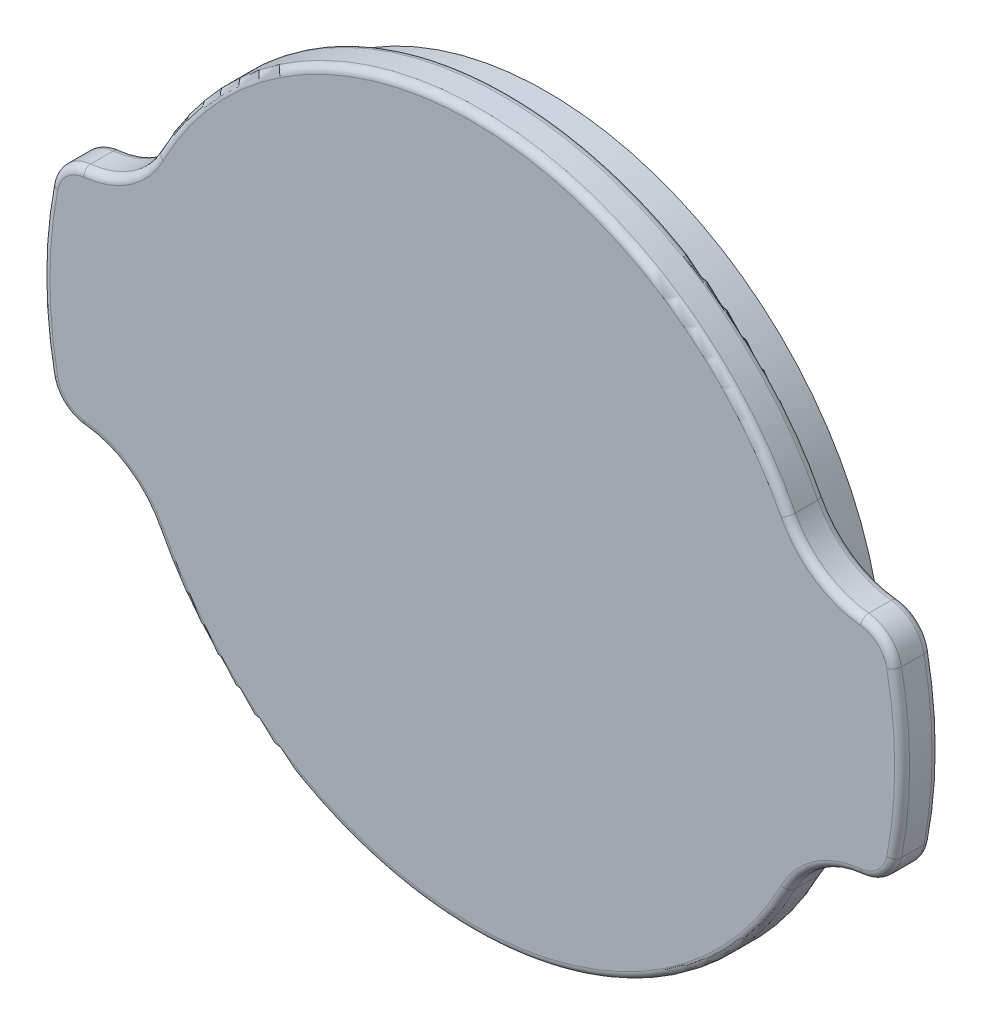
SolidWorks part; units mm, degrees
ref_plane "Front Plane" through (0, 0, 0) normal (0, 0, 1) x (1, 0, 0)
ref_plane "Top Plane" through (0, 0, 0) normal (0, 1, 0) x (1, 0, 0)
ref_plane "Right Plane" through (0, 0, 0) normal (1, 0, 0) x (0, 0, -1)
sketch "hopperTankCover" plane through (0, 0, 0) normal (0, 0, 1) x (1, 0, 0)
  circle A0 centre (0, 0) radius 95 construction
  circle A1 centre (0, 0) radius 95
extrude "Boss-Extrude1" add sketch "hopperTankCover" along normal blind 10
sketch "hopperTankCoverLip" plane through (0, 0, 0) normal (0, 0, -1) x (-1, 0, 0)
  circle A4 centre (0, 0) radius 85
  circle A5 centre (0, 0) radius 85
  circle A7 centre (0, 0) radius 89.9
  circle A8 centre (0, 0) radius 89.9
  dimension "hopperTankWallThickness" = 5
  dimension "generalFittingTolerance" = 0.1
extrude "Boss-Extrude2" add sketch "hopperTankCoverLip" along normal blind 10
sketch "hopperTankCoverHandle" plane through (0, 0, 10) normal (0, 0, 1) x (1, 0, 0)
  line L0 (-111.018, 30) -> (-90.1388, 30)
  line L1 (-111.018, -30) -> (-90.1388, -30)
  line L2 (0, 0) -> (0, 51.9864) construction
  line L3 (111.018, -30) -> (90.1388, -30)
  line L4 (111.018, 30) -> (90.1388, 30)
  arc A0 (90.1388, 30) -> (90.1388, -30) centre (0, 0) cw
  circle A1 centre (0, 0) radius 95 construction
  circle A2 centre (0, 0) radius 115
  arc A3 (-111.018, 30) -> (-111.018, -30) centre (0, 0) ccw
  arc A4 (-90.1388, 30) -> (-90.1388, -30) centre (0, 0) ccw
  arc A5 (111.018, 30) -> (111.018, -30) centre (0, 0) cw
  dimension "hopperTankCoverHandleLength" = 30
  dimension "D1" = 20
extrude "Boss-Extrude3" add sketch "hopperTankCoverHandle" against normal blind 10
fillet "Fillet1" radius 25 4 edges at (90.1388, -30, 5) (90.1388, 30, 5) (-90.1388, 30, 5) (-90.1388, -30, 5)
fillet "Fillet3" radius 10 4 edges at (-111.018, -30, 5) (-111.018, 30, 5) (111.018, 30, 5) (111.018, -30, 5)
fillet "Fillet4" radius 2 24 edges at (0, -95, 10) (0, -95, 0) (0, 95, 0) (0, 95, 10) (92.5575, -34.353, 10) (92.5575, 34.353, 0) (-92.5575, 34.353, 10) (-92.5575, -34.353, 0) (-115, 0, 10) (-115, 0, 0) (92.5575, 34.353, 10) (-92.5575, -34.353, 10) (115, 0, 10) (109.7868, -27.5691, 10) (109.7868, 27.5691, 10) (-109.7868, 27.5691, 10) (-109.7868, -27.5691, 10) (115, 0, 0) (92.5575, -34.353, 0) (-92.5575, 34.353, 0) (109.7868, -27.5691, 0) (109.7868, 27.5691, 0) (-109.7868, 27.5691, 0) (-109.7868, -27.5691, 0)
equation "\"pelletWidth\"= 13mm'The Width of the pellet to be dispensed"
equation "\"pelletLength\"= 26mm'The length of the pellet to be dispensed"
equation "\"pelletThickness\"= 13mm'The Thickness of the pellet to be dispensed"
equation "\"pelletRadius\"= 10mm'The roundness / radius of the pellet to be dispensed"
equation "\"rotatingPlateDiameter\"= 100mm'the diameter of the rotating plate"
equation "\"rotatingPlateHeight\"= (\"pelletThickness\"*0.9)'The thickness of the rotating plate"
equation "\"rotatingPlateDiameterAllowance\"= 0.5mm'Allowance around the edge of the rotating plate"
equation "\"rotatingPlateAgitatorDiameter\"= ( \"rotatingPlateDiameter\"-((\"pelletWidth\"*1.3)*2.5) )'The diameter of the \"agitator\" section of the rotating plate"
equation "\"rotatingPlateAgitatorHeight\"= 80mm'The height of the \"agitator\" section of the rotating plate"
equation "\"rotatingPlateAgitatorBladeThickness\"= 4mm'The thickness of the blade on the \"agitator\" section of the rotating plate"
equation "\"rotatingPlateAgitatorBladeDistance\"= ( (\"rotatingPlateAgitatorDiameter\"+ 20mm) - (\"rotatingPlateAgitatorDiameter\") )'The distance offset of the blade from the surface of the \"agitator\" section of the rotating plate"
equation "\"rotatingPlateAgitatorBladeBottomGap\"= ( \"pelletThickness\"*1.2 )'The gap between the bottom of the blade and the base of the plate on the \"agitator\" section of the rotating plate"
equation "\"rotatingPlateAgitatorBladesNumber\"= ( 3 )'The number of blades on the \"agitator\" section of the rotating plate"
equation "\"hopperBaseChamferAngle\"= 60deg'Angle of the chamfer of the Hopper base Toward the plate"
equation "\"hopperBaseLipOverhang\"= 5mm'The overhang amount of the hopper base lip"
equation "\"hopperBaseLipDepth\"= 5mm'The depth of the hopper base's overhang lip"
equation "\"hopperBaseLockNotchWidth\"= 10mm'The width of the hopper base \"lock\" notch to prevent rotation"
equation "\"hopperBaseLockNotchHeight\"= 10mm'The height of the hopper base \"lock\" notch to prevent rotation"
equation "\"hopperBaseRearNotchHeight\"= 8mm'The height of the rear snap-lock notch on the hopper base"
equation "\"hopperBaseRearNotchWidth\"= 8mm'The width of the rear snap-lock notch on the hopper base"
equation "\"hopperTankWallThickness\"= 5mm'The wall thickness of the hopper tank where pellet reserve will be stored"
equation "\"hopperTankDiameter\"= ( \"rotatingPlateDiameter\"*1.8 )'**Must be greater than \"rotatingPlateDiameter\" -- The inner diameter of the hopper tank where pellet reserve will be stored"
equation "\"hopperTankHeight\"= 200mm'The height of the hopper tank where pellet reserve will be stored"
equation "\"hopperTankCoverThickness\"= 10mm'The thickness of the Hopper Tank's cover"
equation "\"motorMountOffset\"= 30mm'The distance offset of the motor mount part from the hopper tank's outer edge"
equation "\"motorMountHeight\"= (\"motorHeight\" + \"motorFacePlateThickness\" + 0mm)'The height / thickness of the motor mount part"
equation "\"motorDiameter\"= 35mm'The Diameter of the main motor unit"
equation "\"motorHeight\"= 13.4mm'The height of the main motor unit"
equation "\"motorConnectorWidth\"= 10mm'The width of the motor's electrical cable connector"
equation "\"motorConnectorLength\"= 8mm'The length of the motor's electrical cable connector"
equation "\"motorConnectorHeight\"= 5mm'The height of the motor's electrical cable connector"
equation "\"motorFacePlateLength\"= 50mm'The length of the motor faceplate"
equation "\"motorFacePlateWidth\"= 10mm'The width of the motor faceplate"
equation "\"motorFacePlateThickness\"= 1mm'The thickness of the motor faceplate"
equation "\"motorFacePlateCenterRadius\"= 20mm'The rounding radius of the motor faceplate center"
equation "\"motorFacePlateEndRadius\"= 10mm'The rounding radius of the motor faceplate ends"
equation "\"motorFacePlateMountingHoleDiameter\"= 6mm'The diameter of the motor faceplate's mounting holes"
equation "\"motorFacePlateMoutingHoleDistanceBetweenHoles\"= 42mm'The distance between the center of the mounting holes"
equation "\"motorSpindleDiameter\"= 2mm'The diameter of the motor spindle"
equation "\"motorSpindleFlatFaceLength\"= 1.5mm'The length of the flat face of the motor spindle"
equation "\"motorSpindleHeight\"= 9mm'The height of the motor spindle from the face of the motor"
equation "\"motorSpindleMountDiameter\"= 12mm'The diameter of the raised mount section of the motor where the spindle is attached"
equation "\"motorSpindleMountHeight\"= 1.5mm'The height of the raised mount section of the motor where the spindle is attached"
equation "\"generalFittingTolerance\"= 0.1mm'The general fitting tolerance between contacting parts"
equation "\"D1@Boss-Extrude1\"= \"hopperTankCoverThickness\""
equation "\"generalFittingTolerance@hopperTankCoverLip\" = \"generalFittingTolerance\""
equation "\"hopperTankWallThickness@hopperTankCoverLip\" = \"hopperTankWallThickness\""
equation "\"D1@Boss-Extrude2\"=\"hopperTankCoverThickness\""
equation "\"D1@Boss-Extrude3\"=\"hopperTankCoverThickness\""
equation "\"hopperTankCoverHandleLength\"= 60mm'The length of the handles on the hopper tank cover"
equation "\"hopperTankCoverHandleWidth\"= 20mm'The width of the handles on the hopper tank cover, defined as the offset from the cover's main edge"
equation "\"hopperTankCoverHandleLength@hopperTankCoverHandle\" = \"hopperTankCoverHandleLength\" / 2"
equation "\"D1@hopperTankCoverHandle\" = \"hopperTankCoverHandleWidth\""
equation "\"rotatingPlatePelletSlotLength\"= \"pelletLength\"*1.3'The length of the slot where a pellet will be captured"
equation "\"rotatingPlatePelletSlotWidth\"= \"pelletWidth\"*1.3'The width of the slot where a pellet will be captured"
equation "\"rotatingPlateNumberOfPelletSlots\"= ( (2*pi*(\"rotatingPlateDiameter\"/2)) / ((\"rotatingPlatePelletSlotLength\"*1.1)*3) )'The maximum number of pellet slots allows in the rotating plate for proper spacing"
equation "\"rotatingPlateAgitatorTopRoundingRadius\"= 6mm'The rounding radius of the top of the \"agitator\" section of the rotating plate"
equation "\"hopperBaseInnerDiameter\"= (\"rotatingPlateDiameter\") + (\"rotatingPlateDiameterAllowance\"*2)'Diameter of the Base of the hopper where it meets the motor mount + rotating plate"
equation "\"hopperBaseOuterDiameter\"= (\"hopperBaseInnerDiameter\" + (\"hopperTankWallThickness\"*2) + 60mm)'Diameter of the Base of the hopper where it meets the motor mount + rotating plate"
equation "\"hopperBasePelletBlockerMountingSlotWidth\"= 5mm'The width of the pellet blocker mounting slot on the hopper base"
equation "\"hopperBasePelletBlockerMountingSlotOffsetFromTopOfChamfer\"= 15mm'The distance offset of the top of the pellet blocker mounting slot from the top of the hopper base chamfer"
equation "\"hopperBasePelletBlockerMountingSlotOffsetFromBottomOfChamfer\"= 10mm'The distance offset of the bottom of the pellet blocker mounting slot from the bottom of the hopper base chamfer"
equation "\"motorMountPelletThroughHoleLength\"= 40mm'The length of the pellet throughhole that routes through the motor mount and other parts"
equation "\"motorMountPelletThroughHoleWidth\"= 20mm'The width of the pellet throughhole that routes through the motor mount and other parts"
equation "\"irBeamUnitLength\"=20mm'The legth of the IR beam unit"
equation "\"irBeamUnitWidth\"=10mm'The width of the IR beam unit"
equation "\"irBeamUnitHeight\"=8mm'The height of the IR beam unit"
equation "\"irBeamUnitSlotWidth\"=2.03mm'The width of the slots on the outside of the IR beam unit"
equation "\"irBeamUnitSlotLength\"=5.10mm'The length of the slots of the outside of the IR beam unit"
equation "\"irBeamUnitSlotDepth\"=0.76mm'The depth of the slots on the outside of the IR beam unit"
equation "\"irBeamUnitSlotChamferAngle\"=45deg'The angle of the \"end\" of the slot on the outside of the IR beam unit"
equation "\"irBeamUnitSideSlotsDistanceFromBottom\"=3.98mm'The distance of the side slots on the outside of the IR beam unit from the bottom edge of the unit"
equation "\"irBeamUnitMountHoleDistanceFromBottom\"=5mm'The distance of the center mounting throughhole of the IR beam unit from the bottom edge of the unit"
equation "\"irBeamUnitMountHoleDiameter\"=2.40mm'The diameter of the center mounting throughhole of the IR beam unit"
equation "\"irBeamUnitMountHoleChamferDiameter\"=5.30mm'The diameter of the chamfer of the center mounting throughole of the IR beam unit"
equation "\"irBeamUnitMountHoleChamferDepth\"=2.65mm'The depth of the chamfer of the center mounting throughole of the IR beam unit"
equation "\"irBeamUnitLEDDistanceFromBottom\"=15mm'The distance of the center of the LED from the bottom edge of the IR beam unit"
equation "\"irBeamUnitLEDMountDiameter\"=8mm'The diameter of the LED mounting base of the IR beam unit"
equation "\"irBeamUnitLEDMountHeight\"=1.02mm'The height of the LED mounting base of the IR beam unit"
equation "\"irBeamUnitLEDDiameter\"=3.00mm'The diameter of the LED of the IR beam unit"
equation "\"irBeamUnitLEDFlatSectionHeight\"=0.65mm'The height of the \"flat\" section of the LED of the IR beam unit"
equation "\"irBeamUnitLEDDomeSectionDiameter\"=\"irBeamUnitLEDDiameter\"'The diameter of the \"domed\" section of the LED of the IR beam unit"
equation "\"irBeamUnitMountingPlateThickness\"=2mm'The thickness of the IR beam unit mounting plate"
equation "\"irBeamUnitMountingPlateAdjustmentSlotLength\"=10mm'The length of the variable/adjustable mounting slot of the IR beam unit mounting plate"
equation "\"pelletBlockerBaseWidth\"= (\"rotatingPlatePelletSlotWidth\"+\"rotatingPlateDiameterAllowance\")*1.1'The width of the base of the pellet blocker where it meets the rotating plate & pellet slot"
equation "\"pelletBlockerBaseLength\"= \"rotatingPlatePelletSlotLength\"*1.1'The length of the base of the pellet blocker where it meets the rotating plate & pellet slot"
equation "\"pelletBlockerBaseRoundingRadius\"= \"pelletWidth\"*0.5'The rounding radius of the base of the pellet blocker where it meets the rotating plate & pellet slot"
equation "\"pelletBlockerBaseHeight\"= \"rotatingPlateAgitatorBladeBottomGap\"*0.75'The height of the base of the pellet blocker where it meets the rotating plate & pellet slot"
equation "\"pelletBlockerNeckLength\"= 50mm'The length of the neck of the pellet blocker"
equation "\"pelletBlockerNeckTopRoundingRadius\"=2mm'The rounding radius of the top of the neck of the pellet blocker"
equation "\"pelletOutletTrackMountingPlateThickness\"= 2mm'The thickness of the Pellet Outlet Track Mounting Plate"
equation "\"pelletOutletTrackMountingPlateHingeHeight\"= (\"irBeamUnitWidth\" + \"irBeamUnitMountingPlateThickness\" + 2mm )'The height of the bottom of the hinge of the Pellet Outlet Mounting Plate"
equation "\"pelletOutletTrackMountingPlateHingeDiameter\"= 6mm'The inner diameter of the hinge on the Pellet Outlet Mounting Plate"
equation "\"pelletOutletTrackMountingPlateHingeOffsetFromHoleDistance\"= (\"pelletOutletTrackMountingPlateHingeDiameter\" + \"pelletOutletTrackMountingPlateThickness\" + 4mm)'The distance offset of the hinge of the Pellet Outlet Mounting Plate from the plate's mounting hole position"
equation "\"pelletOutletTrackHingeWidth\"= 10mm'The width of the pellet outlet track's hinge which mates with the hinge on the mounting plate"
equation "\"pelletOutletTrackHingeOffsetFromIRBeamUnitEdge\"= 6mm'The distance offset of the pelletOutletTrack's mating hinge from the edge of the IR Beam Unit"
equation "\"pelletOutletTrackEndingWidth\"= 50mm'The width of the pellet outlet Track at the end of the Track"
equation "\"pelletOutletTrackEndingLength\"= 30mm'The length of pellet outlet Track at the end of the Track"
equation "\"pelletOutletTrackWallHeight\"= 15mm'The height of the side walls of the pellet outlet Track"
equation "\"pelletOutletTrackThickness\"= 2mm'The thickness of the pellet outlet Track"
equation "\"baseStandMountingFaceHeight\"= 10mm'The height / thickness of the mounting face between the Base Stand and the Motor Mount parts"
equation "\"baseStandOpeningAngle\"= 55deg'The angle of the opening in the front of the Base Stand to allow for unobstructed pellet outlet"
equation "\"baseStandWallThickness\"= 10mm'The wall thickness of the Base Stand"
equation "\"baseStandHeight\"= 100mm'The overall height of the Base Stand part"
equation "\"baseStandFootDiameterOffset\"= 40mm'The distance offset of the Base Stand's foot ring"
equation "\"baseStandFootHeight\"= 20mm'The height / thickness of the Base Stand's foot ring"
